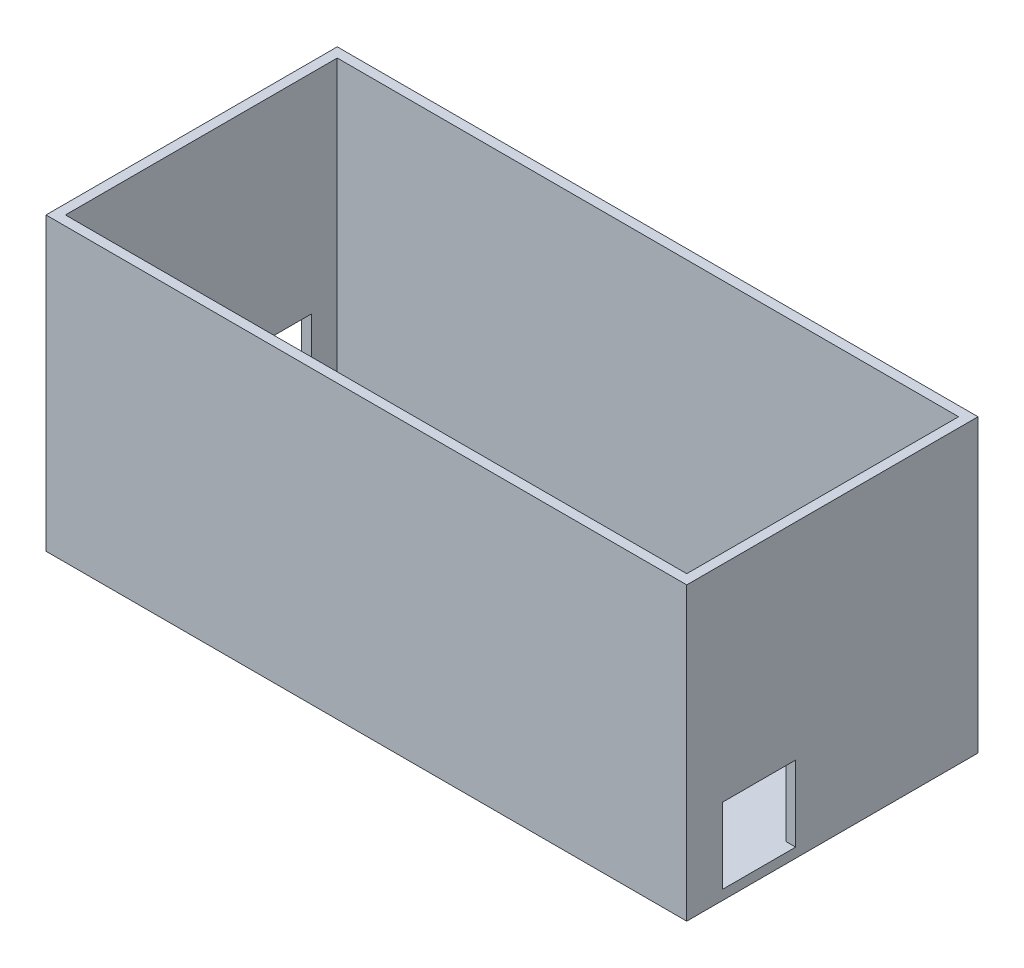
SolidWorks part; units mm, degrees
ref_plane "Plan de face" through (0, 0, 0) normal (0, 0, 1) x (1, 0, 0)
ref_plane "Plan de dessus" through (0, 0, 0) normal (0, 1, 0) x (1, 0, 0)
ref_plane "Plan de droite" through (0, 0, 0) normal (1, 0, 0) x (0, 0, -1)
sketch "Esquisse1" plane through (0, 0, 0) normal (0, 1, 0) x (1, 0, 0)
  line L1 (0, 0) -> (132, 0)
  line L2 (0, 0) -> (0, 60)
  line L3 (0, 60) -> (132, 60)
  line L4 (132, 0) -> (132, 60)
  dimension "D1" = 132
  dimension "D2" = 60
extrude "Boss.-Extru.1" add sketch "Esquisse1" along normal blind 60
shell "Coque1" thickness 2
sketch "Esquisse2" plane through (2, 0, 0) normal (1, 0, 0) x (0, 0, -1)
  line L0 (58, 2) -> (2, 2) construction
  line L1 (52.6623, 2) -> (37.3922, 2)
  line L2 (52.6623, 2) -> (52.6623, 17.0062)
  line L3 (52.6623, 17.0062) -> (37.3922, 17.0062)
  line L4 (37.3922, 2) -> (37.3922, 17.0062)
extrude "Enlèv. mat.-Extru.3" cut sketch "Esquisse2" against normal blind 150
sketch "Esquisse3" plane through (130, 0, 0) normal (-1, 0, 0) x (0, 0, 1)
  line L0 (-2, 2) -> (-58, 2) construction
  line L1 (-7.3176, 2) -> (-22.4318, 2)
  line L2 (-7.3176, 2) -> (-7.3176, 17.5421)
  line L3 (-7.3176, 17.5421) -> (-22.4318, 17.5421)
  line L4 (-22.4318, 2) -> (-22.4318, 17.5421)
extrude "Enlèv. mat.-Extru.4" cut sketch "Esquisse3" against normal blind 150
